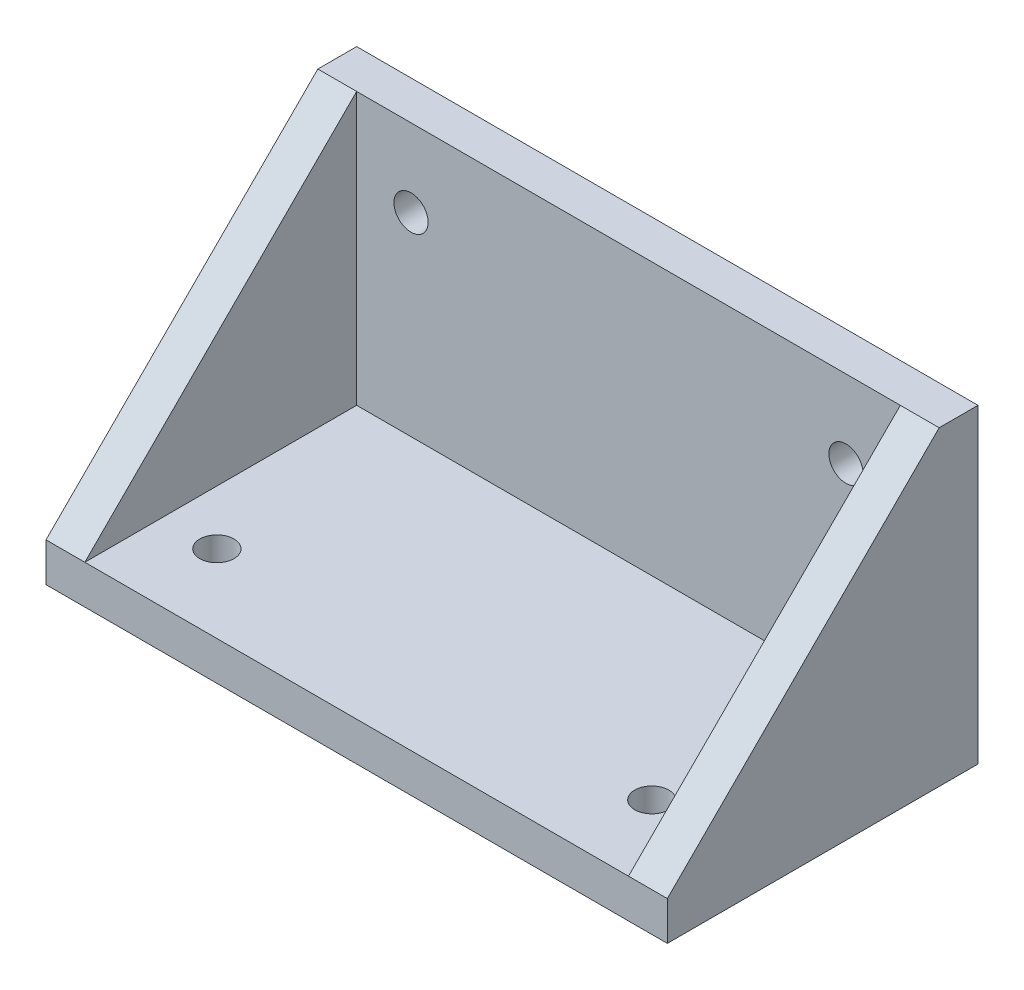
SolidWorks part; units mm, degrees
ref_plane "Front Plane" through (0, 0, 0) normal (0, 0, 1) x (1, 0, 0)
ref_plane "Top Plane" through (0, 0, 0) normal (0, 1, 0) x (1, 0, 0)
ref_plane "Right Plane" through (0, 0, 0) normal (1, 0, 0) x (0, 0, -1)
sketch "Sketch1" plane through (0, 0, 0) normal (0, 1, 0) x (1, 0, 0)
  line L1 (-40, -20) -> (40, -20)
  line L2 (-40, -20) -> (-40, 20)
  line L3 (-40, 20) -> (40, 20)
  line L4 (40, -20) -> (40, 20)
  line L5 (-40, -20) -> (40, 20) construction
  line L6 (-40, 20) -> (40, -20) construction
  point P0 (0, 0)
  dimension "D1" = 80
  dimension "D2" = 40
extrude "Boss-Extrude1" add sketch "Sketch1" along normal blind 5
sketch "Sketch2" plane through (0, 5, 0) normal (0, 1, 0) x (1, 0, 0)
  line L0 (-40, 20) -> (-40, -20) construction
  line L1 (40, 20) -> (-40, 20)
  line L2 (40, 20) -> (40, 15)
  line L3 (40, 15) -> (-40, 15)
  line L4 (-40, 20) -> (-40, 15)
  dimension "D1" = 5
extrude "Boss-Extrude2" add sketch "Sketch2" along normal blind 35
sketch "Sketch3" plane through (-40, 0, 0) normal (-1, 0, 0) x (0, 0, 1)
  line L0 (-15, 40) -> (20, 5)
  line L1 (20, 5) -> (-15, 5)
  line L2 (-15, 40) -> (-15, 5)
extrude "Boss-Extrude3" add sketch "Sketch3" against normal blind 5
sketch "Sketch4" plane through (40, 0, 0) normal (1, 0, 0) x (0, 0, -1)
  line L0 (15, 40) -> (-20, 5)
  line L1 (-20, 5) -> (15, 5)
  line L2 (15, 5) -> (15, 40)
extrude "Boss-Extrude4" add sketch "Sketch4" against normal blind 5
sketch "Sketch5" plane through (0, 5, 0) normal (0, 1, 0) x (1, 0, 0)
  line L0 (40, 20) -> (-40, 20) construction
  line L1 (-40, -20) -> (-40, 15) construction
  line L2 (0, 0) -> (0, -13.0608) construction
  circle A0 centre (-28, -10) radius 2.2
  circle A1 centre (28, -10) radius 2.2
  dimension "D2" = 4.4
  dimension "D1" = 30
  dimension "D3" = 12
extrude "Cut-Extrude1" cut sketch "Sketch5" against normal through all
sketch "Sketch6" plane through (0, 0, -15) normal (0, 0, 1) x (1, 0, 0)
  line L0 (-40, 0) -> (40, 0) construction
  line L1 (-40, 5) -> (-40, 40) construction
  line L2 (0, 0) -> (0, 18.0603) construction
  circle A0 centre (-28, 30) radius 2.2
  circle A1 centre (28, 30) radius 2.2
  dimension "D1" = 4.4
  dimension "D2" = 30
  dimension "D3" = 12
extrude "Cut-Extrude2" cut sketch "Sketch6" against normal through all
